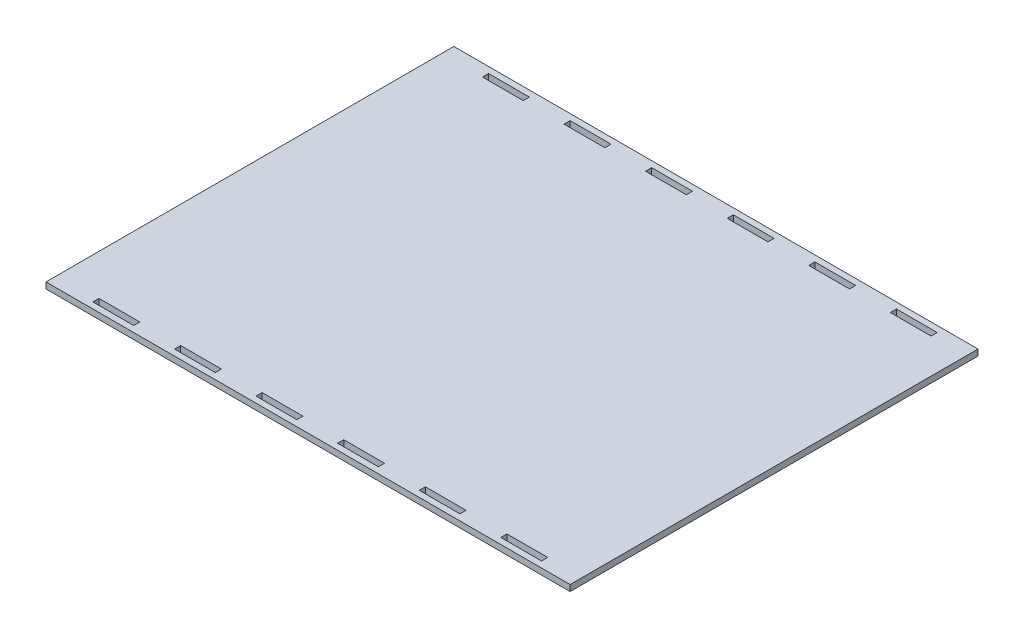
SolidWorks part; units mm, degrees
ref_plane "Plan de face" through (0, 0, 0) normal (0, 0, 1) x (1, 0, 0)
ref_plane "Plan de dessus" through (0, 0, 0) normal (0, 1, 0) x (1, 0, 0)
ref_plane "Plan de droite" through (0, 0, 0) normal (1, 0, 0) x (0, 0, -1)
sketch "Esquisse1" plane through (0, 0, 0) normal (0, 1, 0) x (1, 0, 0)
  line L0 (-68.5, -94) -> (-68.5, -97)
  line L1 (128.5, 100) -> (-128.5, 100)
  line L2 (128.5, 100) -> (128.5, -100)
  line L3 (128.5, -100) -> (-128.5, -100)
  line L4 (-128.5, 100) -> (-128.5, -100)
  line L5 (128.5, 100) -> (-128.5, -100) construction
  line L6 (128.5, -100) -> (-128.5, 100) construction
  line L7 (-108.5, -94) -> (-88.5, -94)
  line L8 (-108.5, -94) -> (-108.5, -97)
  line L9 (-108.5, -97) -> (-88.5, -97)
  line L10 (-88.5, -94) -> (-88.5, -97)
  line L11 (-68.5, -94) -> (-48.5, -94)
  line L12 (-48.5, -94) -> (-48.5, -97)
  line L13 (-68.5, -97) -> (-48.5, -97)
  line L14 (-28.5, -94) -> (-28.5, -97)
  line L15 (-28.5, -94) -> (-8.5, -94)
  line L16 (-8.5, -94) -> (-8.5, -97)
  line L17 (-28.5, -97) -> (-8.5, -97)
  line L18 (11.5, -94) -> (11.5, -97)
  line L19 (11.5, -94) -> (31.5, -94)
  line L20 (31.5, -94) -> (31.5, -97)
  line L21 (11.5, -97) -> (31.5, -97)
  line L22 (51.5, -94) -> (51.5, -97)
  line L23 (51.5, -94) -> (71.5, -94)
  line L24 (71.5, -94) -> (71.5, -97)
  line L25 (51.5, -97) -> (71.5, -97)
  line L26 (91.5, -94) -> (91.5, -97)
  line L27 (91.5, -94) -> (111.5, -94)
  line L28 (111.5, -94) -> (111.5, -97)
  line L29 (91.5, -97) -> (111.5, -97)
  line L30 (0, 0) -> (-128.5, 0) construction
  line L31 (91.5, 97) -> (111.5, 97)
  line L32 (111.5, 94) -> (111.5, 97)
  line L33 (91.5, 94) -> (111.5, 94)
  line L34 (91.5, 94) -> (91.5, 97)
  line L35 (51.5, 97) -> (71.5, 97)
  line L36 (71.5, 94) -> (71.5, 97)
  line L37 (51.5, 94) -> (71.5, 94)
  line L38 (51.5, 94) -> (51.5, 97)
  line L39 (11.5, 97) -> (31.5, 97)
  line L40 (31.5, 94) -> (31.5, 97)
  line L41 (11.5, 94) -> (31.5, 94)
  line L42 (11.5, 94) -> (11.5, 97)
  line L43 (-28.5, 97) -> (-8.5, 97)
  line L44 (-8.5, 94) -> (-8.5, 97)
  line L45 (-28.5, 94) -> (-8.5, 94)
  line L46 (-28.5, 94) -> (-28.5, 97)
  line L47 (-68.5, 97) -> (-48.5, 97)
  line L48 (-48.5, 94) -> (-48.5, 97)
  line L49 (-68.5, 94) -> (-48.5, 94)
  line L50 (-88.5, 94) -> (-88.5, 97)
  line L51 (-108.5, 97) -> (-88.5, 97)
  line L52 (-108.5, 94) -> (-108.5, 97)
  line L53 (-108.5, 94) -> (-88.5, 94)
  line L54 (-68.5, 94) -> (-68.5, 97)
  point P0 (0, 0)
  point P32 (-128.5, 0)
  point P33 (0, 0)
  dimension "D1" = 257
  dimension "D2" = 3
  dimension "D3" = 20
  dimension "D4" = 20
  dimension "D5" = 3
  dimension "D6" = 200
  dimension "D7" = 6
extrude "Boss.-Extru.1" add sketch "Esquisse1" along normal blind 3
